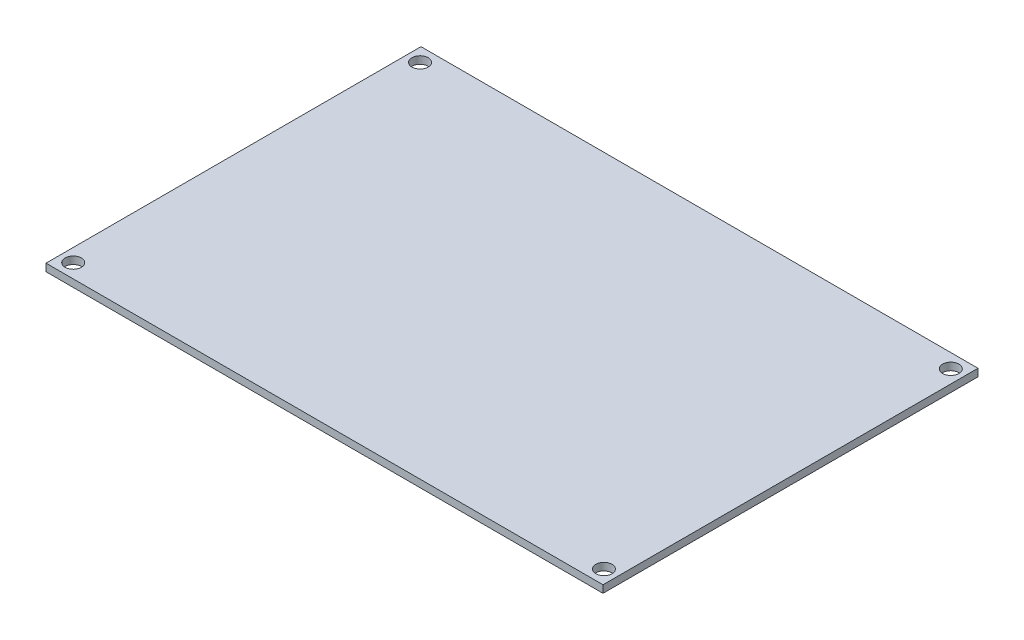
SolidWorks part; units mm, degrees
ref_plane "Front Plane" through (0, 0, 0) normal (0, 0, 1) x (1, 0, 0)
ref_plane "Top Plane" through (0, 0, 0) normal (0, 1, 0) x (1, 0, 0)
ref_plane "Right Plane" through (0, 0, 0) normal (1, 0, 0) x (0, 0, -1)
sketch "Sketch1" plane through (0, 0, 0) normal (0, 1, 0) x (1, 0, 0)
  line L0 (-59.825, 0) -> (59.825, 0) construction
  line L1 (-59.825, 40.275) -> (59.825, 40.275)
  line L2 (-59.825, 40.275) -> (-59.825, -40.275)
  line L3 (-59.825, -40.275) -> (59.825, -40.275)
  line L4 (59.825, 40.275) -> (59.825, -40.275)
  line L5 (-59.825, 40.275) -> (59.825, -40.275) construction
  line L6 (-59.825, -40.275) -> (59.825, 40.275) construction
  line L7 (0, 40.275) -> (0, -40.275) construction
  circle A0 centre (-57, 37.25) radius 1.75
  circle A1 centre (57, 37.25) radius 1.75
  circle A2 centre (57, -37.25) radius 1.75
  circle A3 centre (-57, -37.25) radius 1.75
  point P0 (0, 0)
  dimension "D3" = 3.5
  dimension "D1" = 119.65
  dimension "D2" = 80.55
  dimension "D4" = 114
  dimension "D5" = 74.5
extrude "Boss-Extrude1" add sketch "Sketch1" along normal blind 1.6
